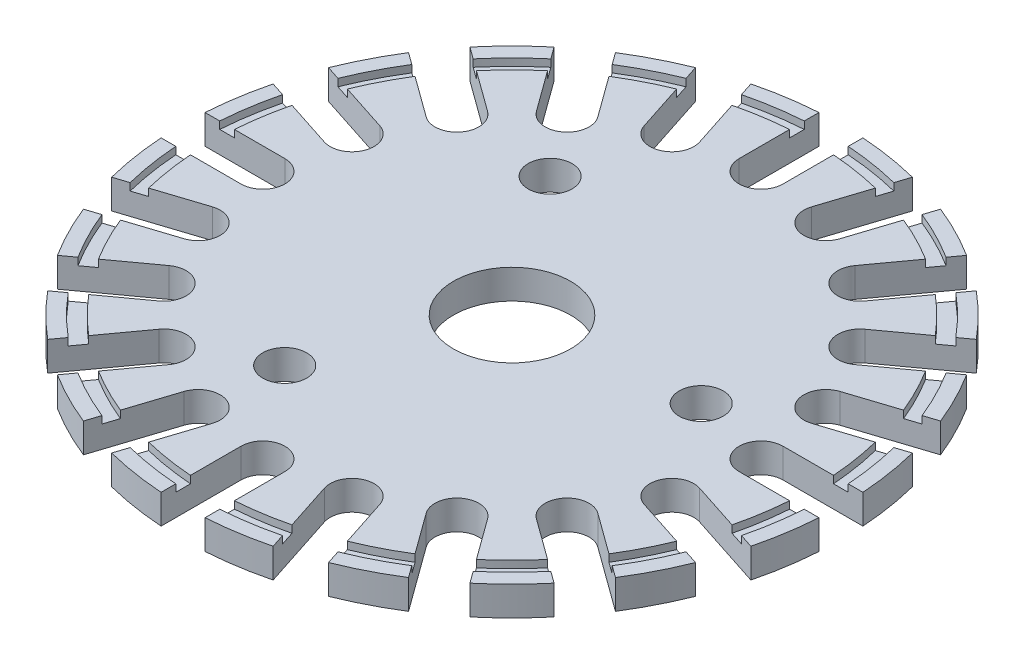
SolidWorks part; units mm, degrees
material "Alloy Steel"
ref_plane "Front Plane" through (0, 0, 0) normal (0, 0, 1) x (1, 0, 0)
ref_plane "Top Plane" through (0, 0, 0) normal (0, 1, 0) x (1, 0, 0)
ref_plane "Right Plane" through (0, 0, 0) normal (1, 0, 0) x (0, 0, -1)
sketch "Sketch1" plane through (0, 0, 0) normal (0, 1, 0) x (1, 0, 0)
  circle A0 centre (0, 0) radius 22.5
  dimension "D1" = 45
extrude "Boss-Extrude1" add sketch "Sketch1" along normal blind 2
sketch "Sketch2" plane through (0, 2, 0) normal (0, 1, 0) x (1, 0, 0)
  line L0 (0, 0) -> (0, 22.5) construction
  line L1 (0, 22.7958) -> (0, 17) construction
  line L2 (1.5, 22.7958) -> (1.5, 17)
  line L3 (-1.5, 22.7958) -> (-1.5, 17)
  circle A0 centre (0, 0) radius 22.5 construction
  arc A1 (1.5, 22.7958) -> (-1.5, 22.7958) centre (0, 22.7958) ccw
  arc A2 (-1.5, 17) -> (1.5, 17) centre (0, 17) ccw
  point P8 (0, 19.8979)
  point P14 (0, 15.5)
  dimension "D1" = 1.5
  dimension "D2" = 7
extrude "Cut-Extrude1" cut sketch "Sketch2" against normal blind 2
pattern_circular "CirPattern1" count 20 every 18 about axis through (0, 0, 0) along (0, 1, 0) of "Cut-Extrude1"
sketch "Sketch3" plane through (0, 2, 0) normal (0, 1, 0) x (1, 0, 0)
  circle A0 centre (0, 0) radius 21.5
  circle A1 centre (0, 0) radius 20.5
  dimension "D1" = 43
  dimension "D2" = 41
extrude "Cut-Extrude2" cut sketch "Sketch3" against normal blind 0.5
sketch "Sketch4" plane through (0, 2, 0) normal (0, 1, 0) x (1, 0, 0)
  circle A0 centre (0, 0) radius 4
  dimension "D1" = 8
extrude "Cut-Extrude3" cut sketch "Sketch4" against normal through all
sketch "Sketch5" plane through (0, 0, 0) normal (0, -1, 0) x (1, 0, 0)
  circle A0 centre (0, 0) radius 11.75 construction
  circle A1 centre (-4.7792, 10.7342) radius 1.5
  circle A2 centre (11.6856, -1.2282) radius 1.5
  circle A3 centre (-6.9065, -9.5059) radius 1.5
  point P11 (0, 0)
  dimension "D1" = 23.5
  dimension "D2" = 3
  dimension "D3" = 3
extrude "Cut-Extrude4" cut sketch "Sketch5" against normal blind 10
